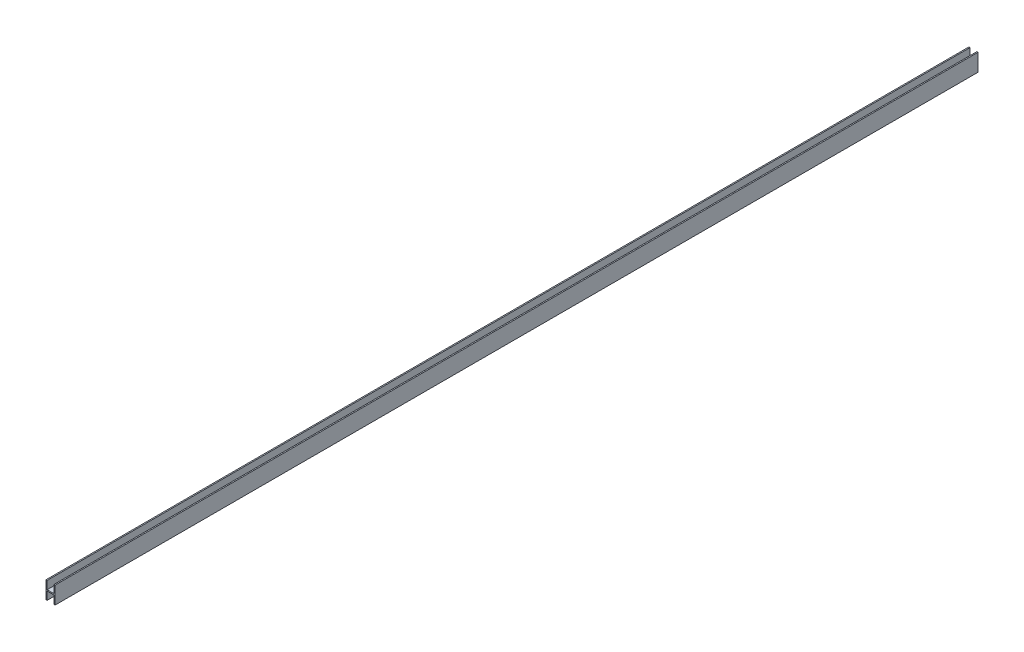
SolidWorks part; units mm, degrees
material "6063-T5"
ref_plane "前视基准面" through (0, 0, 0) normal (0, 0, 1) x (1, 0, 0)
ref_plane "上视基准面" through (0, 0, 0) normal (0, 1, 0) x (1, 0, 0)
ref_plane "右视基准面" through (0, 0, 0) normal (1, 0, 0) x (0, 0, -1)
sketch "草图1" plane through (0, 0, 0) normal (0, 0, 1) x (1, 0, 0)
  line L1 (-4, -7.5) -> (4, -7.5)
  line L2 (-4, -7.5) -> (-4, 7.5)
  line L3 (-4, 7.5) -> (4, 7.5)
  line L4 (4, -7.5) -> (4, 7.5)
  line L5 (-4, -7.5) -> (4, 7.5) construction
  line L6 (-4, 7.5) -> (4, -7.5) construction
  point P0 (0, 0)
  dimension "D1" = 15
  dimension "D2" = 8
extrude "凸台-拉伸1" add sketch "草图1" along normal blind 800
sketch "草图2" plane through (0, 0, 0) normal (0, 0, -1) x (-1, 0, 0)
  line L0 (4, -7.5) -> (-4, -7.5) construction
  line L1 (-3, -14.5) -> (3, -14.5)
  line L2 (-3, -14.5) -> (-3, -0.5)
  line L3 (-3, -0.5) -> (3, -0.5)
  line L4 (3, -14.5) -> (3, -0.5)
  line L5 (-3, -14.5) -> (3, -0.5) construction
  line L6 (-3, -0.5) -> (3, -14.5) construction
  line L7 (-4, 7.5) -> (4, 7.5) construction
  line L8 (-3, 0.5) -> (3, 0.5)
  line L9 (-3, 0.5) -> (-3, 14.5)
  line L10 (-3, 14.5) -> (3, 14.5)
  line L11 (3, 0.5) -> (3, 14.5)
  line L12 (-3, 0.5) -> (3, 14.5) construction
  line L13 (-3, 14.5) -> (3, 0.5) construction
  point P0 (0, -7.5)
  point P7 (0, 7.5)
  dimension "D1" = 6
  dimension "D2" = 6
  dimension "D3" = 0.5
  dimension "D4" = 0.5
extrude "切除-拉伸1" cut sketch "草图2" against normal blind 2400
